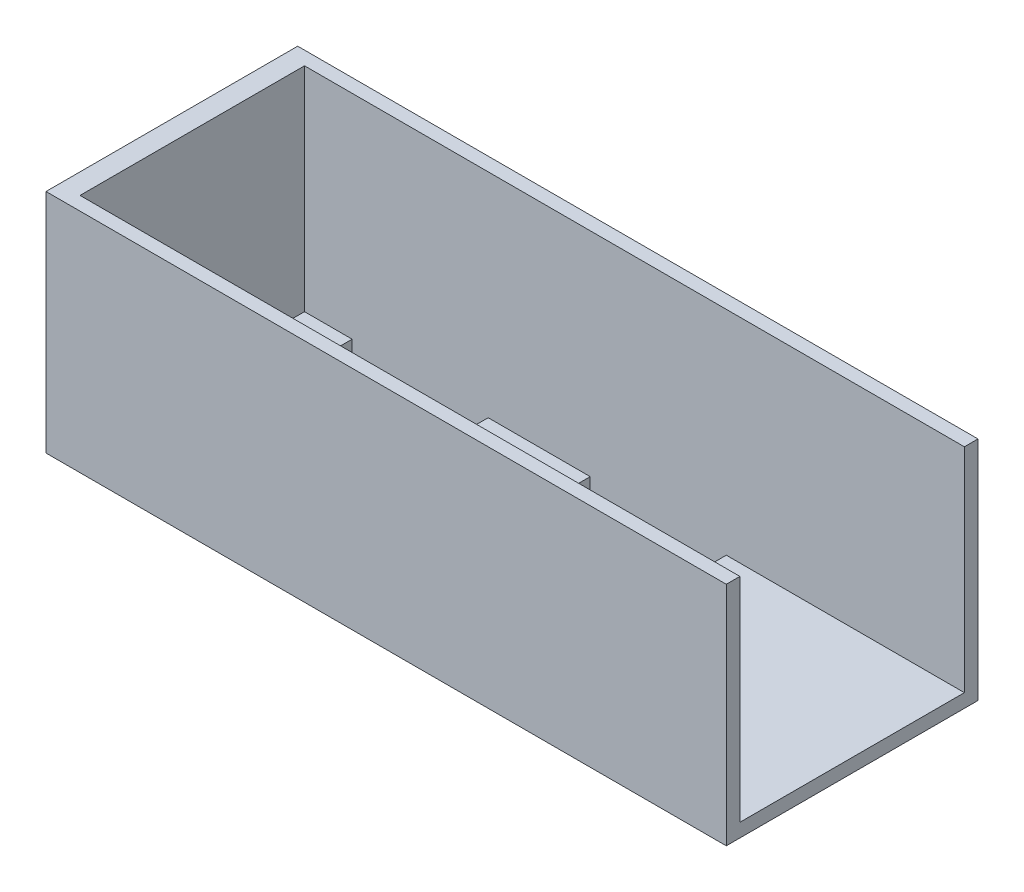
SolidWorks part; units mm, degrees
ref_plane "Front Plane" through (0, 0, 0) normal (0, 0, 1) x (1, 0, 0)
ref_plane "Top Plane" through (0, 0, 0) normal (0, 1, 0) x (1, 0, 0)
ref_plane "Right Plane" through (0, 0, 0) normal (1, 0, 0) x (0, 0, -1)
sketch "Sketch1" plane through (0, 0, 0) normal (1, 0, 0) x (0, 0, -1)
  line L3 (16, 0) -> (18, 0)
  line L25 (-19, -33.3) -> (18, -33.3)
  line L26 (18, -33.3) -> (18, 0)
  line L30 (16, 0) -> (16, -31.3)
  line L32 (-19, 0) -> (-19, -33.3)
  line L33 (-19, 0) -> (-17, 0)
  line L34 (-17, 0) -> (-17, -31.3)
  line L35 (-17, -31.3) -> (16, -31.3)
  dimension "D1" = 2
  dimension "D2" = 2
  dimension "D3" = 31.3
  dimension "D4" = 2
  dimension "D5" = 33
extrude "Boss-Extrude1" add sketch "Sketch1" along normal mid plane 100
sketch "Sketch2" plane through (-50, 0, 0) normal (-1, 0, 0) x (0, 0, 1)
  line L1 (-18, 0) -> (19, 0)
  line L2 (-18, 0) -> (-18, -33.3)
  line L3 (-18, -33.3) -> (19, -33.3)
  line L4 (19, 0) -> (19, -33.3)
extrude "Boss-Extrude2" add sketch "Sketch2" against normal blind 3
sketch "Sketch3" plane through (0, 0, 0) normal (0, 1, 0) x (1, 0, 0)
  line L0 (50, -17) -> (-47, -17) construction
  line L1 (-40, -17) -> (-20, -17)
  line L2 (-40, -17) -> (-40, -10)
  line L3 (-40, -10) -> (-20, -10)
  line L4 (-20, -17) -> (-20, -10)
  line L5 (50, -17) -> (-47, -17) construction
  line L6 (15, -17) -> (-5, -17)
  line L7 (15, -17) -> (15, -10)
  line L8 (15, -10) -> (-5, -10)
  line L9 (-5, -17) -> (-5, -10)
  line L10 (50, 16) -> (-47, 16) construction
  line L11 (-40, 16) -> (-20, 16)
  line L12 (-40, 16) -> (-40, 9)
  line L13 (-40, 9) -> (-20, 9)
  line L14 (-20, 16) -> (-20, 9)
  line L15 (-47, -17) -> (-47, 16) construction
  line L16 (-5, 9) -> (15, 9)
  line L17 (-5, 9) -> (-5, 16)
  line L18 (-5, 16) -> (15, 16)
  line L19 (15, 9) -> (15, 16)
  line L20 (-47, -17) -> (-47, 16) construction
  dimension "D1" = 20
  dimension "D2" = 20
  dimension "D3" = 20
  dimension "D4" = 20
  dimension "D5" = 7
  dimension "D6" = 7
  dimension "D7" = 7
  dimension "D8" = 7
  dimension "D9" = 7
  dimension "D10" = 15
  dimension "D11" = 7
  dimension "D12" = 15
extrude "Cut-Extrude1" cut sketch "Sketch3" against normal blind 50
